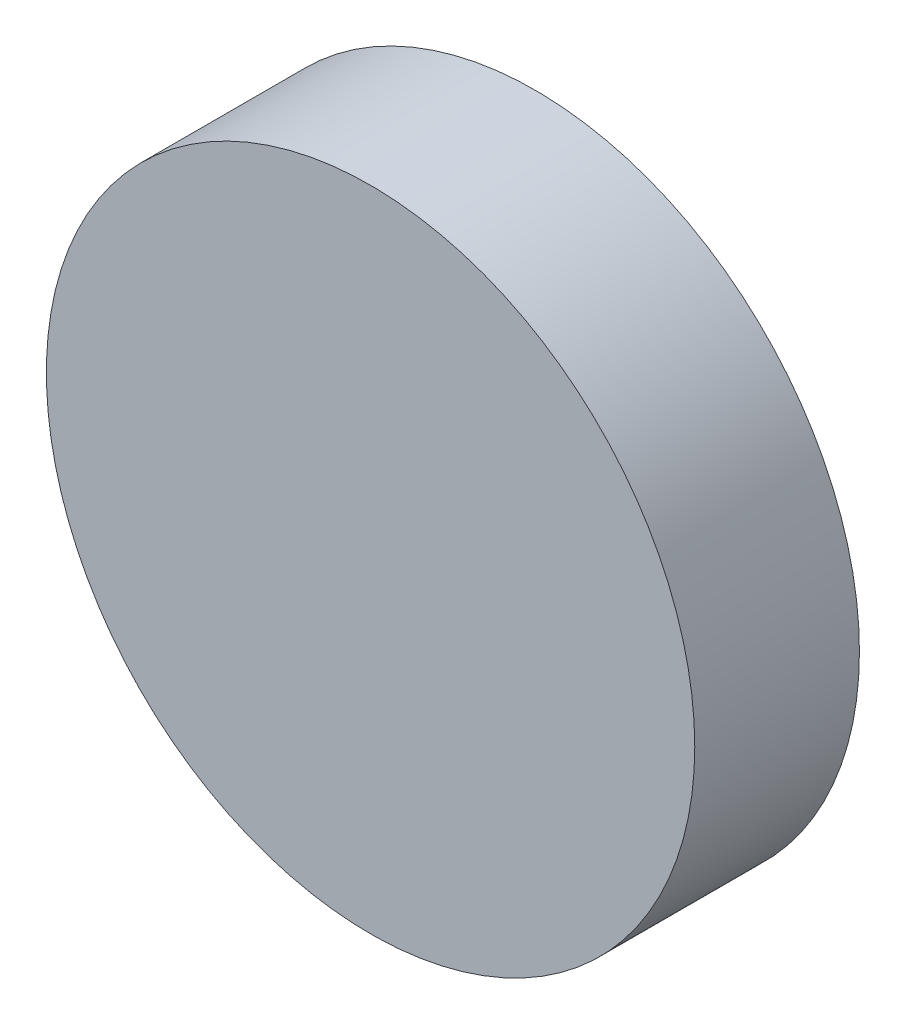
SolidWorks part; units mm, degrees
material "AISI 316 Annealed Stainless Steel Bar (SS)"
ref_plane "Front Plane" through (0, 0, 0) normal (0, 0, 1) x (1, 0, 0)
ref_plane "Top Plane" through (0, 0, 0) normal (0, 1, 0) x (1, 0, 0)
ref_plane "Right Plane" through (0, 0, 0) normal (1, 0, 0) x (0, 0, -1)
sketch "Sketch1" plane through (0, 0, 0) normal (0, 0, 1) x (1, 0, 0)
  circle A0 centre (0, 0) radius 15.75
  dimension "D1" = 31.5
extrude "Boss-Extrude1" add sketch "Sketch1" along normal blind 8
